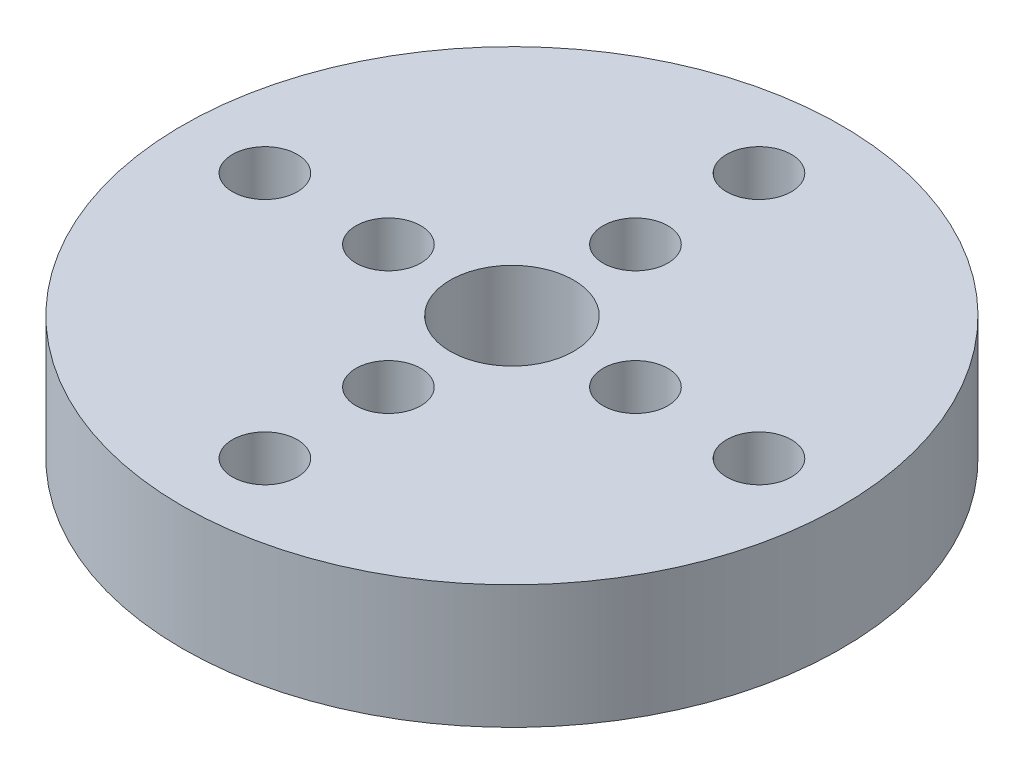
SolidWorks part; units mm, degrees
ref_plane "Front Plane" through (0, 0, 0) normal (0, 0, 1) x (1, 0, 0)
ref_plane "Top Plane" through (0, 0, 0) normal (0, 1, 0) x (1, 0, 0)
ref_plane "Right Plane" through (0, 0, 0) normal (1, 0, 0) x (0, 0, -1)
sketch "스케치1" plane through (0, 0, 0) normal (0, 1, 0) x (1, 0, 0)
  circle A0 centre (0, 0) radius 21.345
extrude "보스-돌출1" add sketch "스케치1" along normal blind 8
sketch "스케치2" plane through (0, 8, 0) normal (0, 1, 0) x (1, 0, 0)
  circle A0 centre (0, 0) radius 4
extrude "컷-돌출1" cut sketch "스케치2" against normal blind 8
sketch "스케치3" plane through (0, 8, 0) normal (0, 1, 0) x (1, 0, 0)
  line L0 (0, 0) -> (0, 50000) construction
  line L1 (0, 0) -> (50000, 0) construction
  circle A0 centre (0, 0) radius 8 construction
  circle A1 centre (0, 0) radius 16 construction
  circle A2 centre (0, 8) radius 2.1
  circle A3 centre (0, 16) radius 2.1
  circle A4 centre (16, 0) radius 2.1
  circle A5 centre (8, 0) radius 2.1
  circle A6 centre (-8, 0) radius 2.1
  circle A7 centre (-16, 0) radius 2.1
  circle A8 centre (0, -8) radius 2.1
  circle A9 centre (0, -16) radius 2.1
extrude "컷-돌출2" cut sketch "스케치3" against normal blind 8
